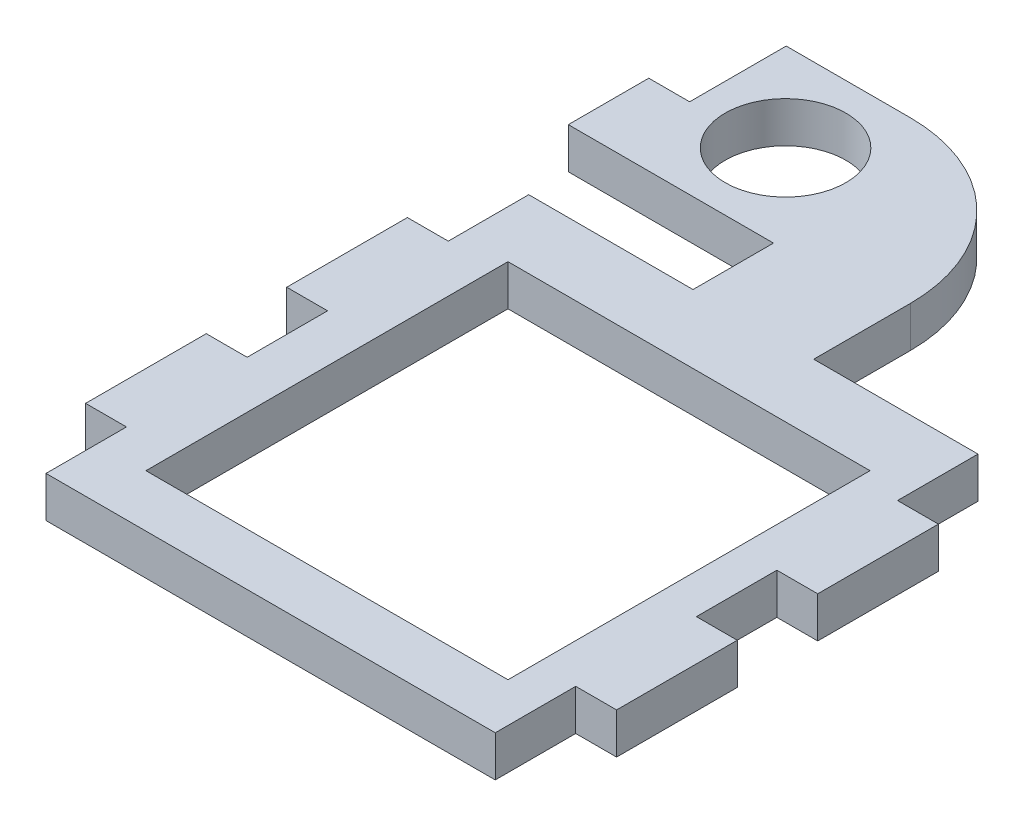
SolidWorks part; units mm, degrees
ref_plane "Front Plane" through (0, 0, 0) normal (0, 0, 1) x (1, 0, 0)
ref_plane "Top Plane" through (0, 0, 0) normal (0, 1, 0) x (1, 0, 0)
ref_plane "Right Plane" through (0, 0, 0) normal (1, 0, 0) x (0, 0, -1)
sketch "Sketch1" plane through (0, 0, 0) normal (0, 1, 0) x (1, 0, 0)
  line L1 (27.92, -30) -> (-27.92, -30)
  line L2 (27.92, -30) -> (27.92, 30)
  line L3 (27.92, 30) -> (-27.92, 30)
  line L4 (-27.92, -30) -> (-27.92, 30)
  line L5 (27.92, -30) -> (-27.92, 30) construction
  line L6 (27.92, 30) -> (-27.92, -30) construction
  line L7 (-22, -23.5) -> (23, -23.5)
  line L8 (-22, -23.5) -> (-22, 21.5)
  line L9 (-22, 21.5) -> (23, 21.5)
  line L10 (23, -23.5) -> (23, 21.5)
  line L11 (-22, -23.5) -> (23, 21.5) construction
  line L12 (-22, 21.5) -> (23, -23.5) construction
  point P0 (0, 0)
  point P6 (0.5, -1)
  dimension "D1" = 55.84
  dimension "D2" = 60
  dimension "D3" = 31
  dimension "D4" = 27.42
  dimension "D5" = 45
extrude "Boss-Extrude1" add sketch "Sketch1" along normal blind 5.08
sketch "Sketch2" plane through (0, 5.08, 0) normal (0, 1, 0) x (1, 0, 0)
  line L0 (-27.92, 30) -> (-27.92, -30) construction
  line L1 (-27.92, -20) -> (-33, -20)
  line L2 (-27.92, -20) -> (-27.92, -5)
  line L3 (-27.92, -5) -> (-33, -5)
  line L4 (-33, -20) -> (-33, -5)
  line L5 (27.92, -30) -> (27.92, 30) construction
  line L6 (27.92, -20) -> (33, -20)
  line L7 (27.92, -20) -> (27.92, -5)
  line L8 (27.92, -5) -> (33, -5)
  line L9 (33, -20) -> (33, -5)
  line L10 (-27.92, 5) -> (-33, 5)
  line L11 (-27.92, 5) -> (-27.92, 20)
  line L12 (-27.92, 20) -> (-33, 20)
  line L13 (-33, 5) -> (-33, 20)
  line L14 (27.92, 5) -> (33, 5)
  line L15 (27.92, 5) -> (27.92, 20)
  line L16 (27.92, 20) -> (33, 20)
  line L17 (33, 5) -> (33, 20)
  dimension "D1" = 10
  dimension "D2" = 15
  dimension "D3" = 5.08
  dimension "D5" = 10
  dimension "D4" = 2
extrude "Boss-Extrude2" add sketch "Sketch2" against normal up to surface (5.08 mm away) up to face at (0, 0, 0)
sketch "Sketch3" plane through (0, 5.08, 0) normal (0, 1, 0) x (1, 0, 0)
  line L0 (27.92, 30) -> (-27.92, 30) construction
  line L1 (-7.5, 30) -> (7.5, 30)
  line L2 (-7.5, 30) -> (-7.5, 40)
  line L3 (-33, 20) -> (-33, 5) construction
  line L4 (7.5, 30) -> (7.5, 40)
  line L5 (-7.5, 30) -> (7.5, 40) construction
  line L6 (-7.5, 40) -> (7.5, 30) construction
  line L8 (-7.5, 40) -> (-33, 40)
  line L9 (7.5, 40) -> (7.5, 62)
  line L10 (7.5, 62) -> (-33, 62)
  line L11 (-33, 40) -> (-33, 62)
  circle A0 centre (-17, 51) radius 7.5
  point P0 (0, 35)
  point P8 (0, 30)
  dimension "D4" = 16
  dimension "D5" = 21
  dimension "D6" = 15
  dimension "D1" = 15
  dimension "D2" = 10
  dimension "D3" = 22
extrude "Boss-Extrude3" add sketch "Sketch3" against normal up to surface (5.08 mm away) up to face at (0, 0, 0)
fillet "Fillet1" radius 20 1 edges at (7.5, 2.54, -62)
sketch "Sketch4" plane through (0, 5.08, 0) normal (0, 1, 0) x (1, 0, 0)
  line L0 (-27.92, 30) -> (-27.92, 20) construction
  line L1 (-33, 62) -> (-27.92, 62)
  line L2 (-33, 62) -> (-33, 50)
  line L3 (-33, 50) -> (-27.92, 50)
  line L4 (-27.92, 62) -> (-27.92, 50)
  line L5 (-33, 40) -> (-7.5, 40) construction
  dimension "D1" = 10
extrude "Cut-Extrude1" cut sketch "Sketch4" against normal through all
